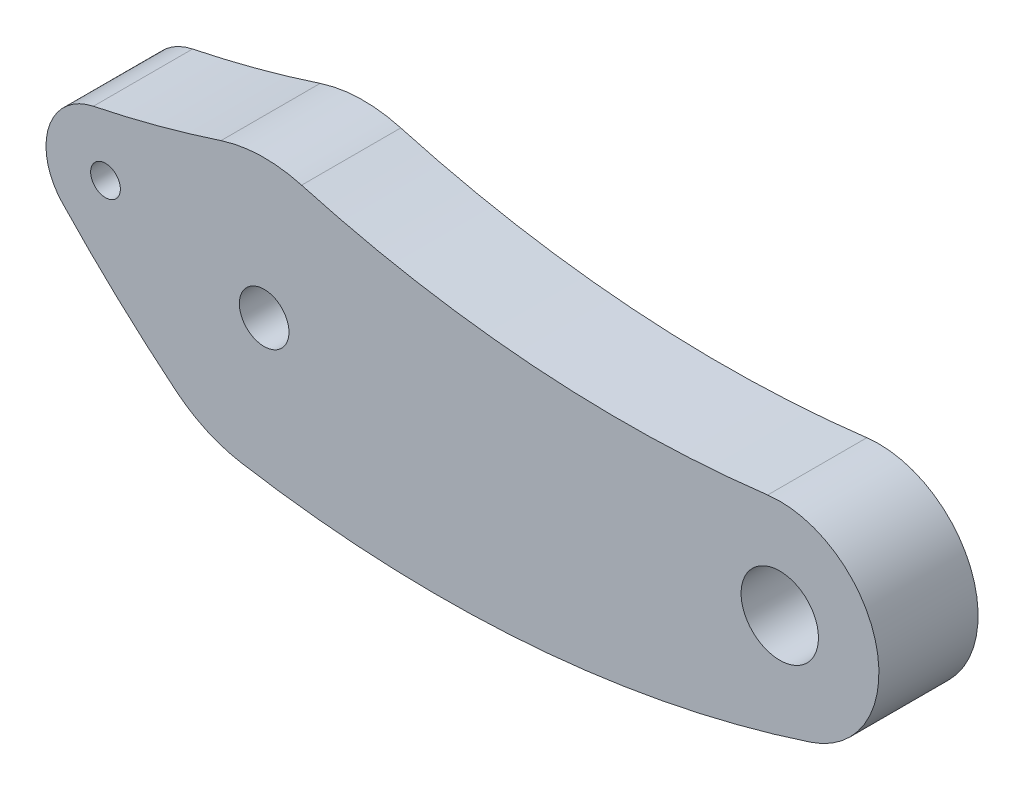
SolidWorks part; units mm, degrees
material "PMMA"
ref_plane "Front Plane" through (0, 0, 0) normal (0, 0, 1) x (1, 0, 0)
ref_plane "Top Plane" through (0, 0, 0) normal (0, 1, 0) x (1, 0, 0)
ref_plane "Right Plane" through (0, 0, 0) normal (1, 0, 0) x (0, 0, -1)
sketch "Sketch1" plane through (0, 0, 0) normal (0, 0, 1) x (1, 0, 0)
  line L0 (0, 0) -> (26, 0) construction
  line L1 (0, 0) -> (-4.4264, -5.4228) construction
  line L2 (0, 0) -> (-1.1684, -6.9018) construction
  line L3 (-0.0094, -0.0557) -> (-0.0094, -9.6429) construction
  line L4 (-0.0094, -0.0557) -> (-10.185, -0.0557) construction
  circle A0 centre (0, 0) radius 1.25
  circle A1 centre (26, 0) radius 1.95
  circle A2 centre (-8, 2) radius 0.75
  arc A3 (-8.611, 4.9371) -> (-10.185, -0.0557) centre (-8, 2) ccw
  arc A4 (27.5594, -4.7506) -> (25.3905, 4.9627) centre (26, 0) ccw
  arc A5 (1.8886, 6.7404) -> (-2.1763, 6.6531) centre (0, 0) ccw
  arc A10 (1.8886, 6.7404) -> (25.3905, 4.9627) centre (18.0769, 64.5153) ccw
  arc A11 (-8.611, 4.9371) -> (-2.1763, 6.6531) centre (-20.8301, 63.6797) ccw
  arc A12 (-10.185, -0.0557) -> (-4.4264, -5.4228) centre (33.5145, 41.0582) ccw
  arc A13 (-1.1684, -6.9018) -> (27.5594, -4.7506) centre (8.8462, 52.2565) ccw
  arc A14 (-4.4264, -5.4228) -> (-1.1684, -6.9018) centre (0, 0) ccw
  dimension "D1" = 2.5
  dimension "D2" = 3.9
  dimension "D6" = 1.5
  dimension "D7" = 6
  dimension "D8" = 10
  dimension "D9" = 14
  dimension "D10" = 60
  dimension "D11" = 60
  dimension "D12" = 60
  dimension "D13" = 60
  dimension "D3" = 26
  dimension "D4" = 8
  dimension "D5" = 2
  dimension "D14" = 29.616
  dimension "D15" = 9.608
  dimension "D16" = 10.185
  dimension "D17" = 4.7506
  dimension "D18" = 0.6095
  dimension "D19" = 1.8886
  dimension "D20" = 2.1763
  dimension "D21" = 8.611
extrude "Boss-Extrude1" add sketch "Sketch1" along normal blind 5
cosmetic thread "Cosmetic Thread1"
cosmetic thread "Cosmetic Thread2"
